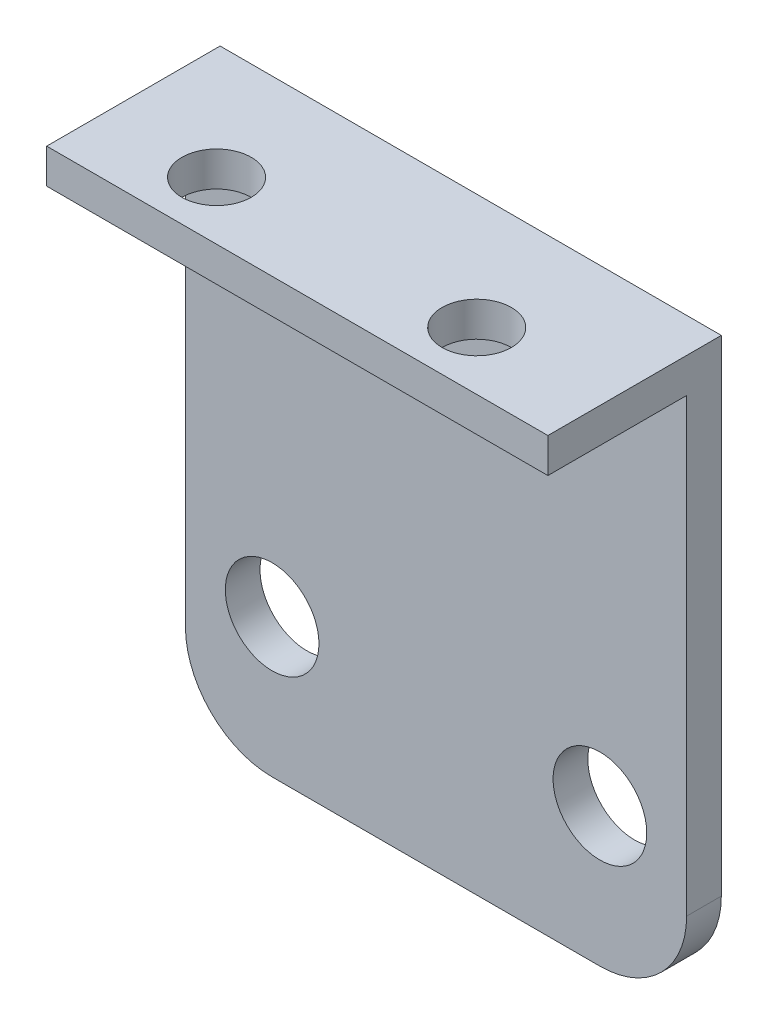
SolidWorks part; units mm, degrees
ref_plane "Front Plane" through (0, 0, 0) normal (0, 0, 1) x (1, 0, 0)
ref_plane "Top Plane" through (0, 0, 0) normal (0, 1, 0) x (1, 0, 0)
ref_plane "Right Plane" through (0, 0, 0) normal (1, 0, 0) x (0, 0, -1)
sketch "Sketch1" plane through (0, 0, 0) normal (0, 0, 1) x (1, 0, 0)
  line L1 (-13.5453, 41.5925) -> (15.3547, 41.5925)
  line L2 (-13.5453, 41.5925) -> (-13.5453, 74.5925)
  line L3 (-13.5453, 74.5925) -> (15.3547, 74.5925)
  line L4 (15.3547, 41.5925) -> (15.3547, 74.5925)
  circle A0 centre (-8.5453, 49.5925) radius 2.7
  circle A1 centre (10.3547, 49.5925) radius 2.7
  dimension "D1" = 5
  dimension "D2" = 5
  dimension "D3" = 8
  dimension "D4" = 25
extrude "Boss-Extrude1" add sketch "Sketch1" along normal blind 2
fillet "Fillet1" radius 5 2 edges at (-13.5453, 41.5925, 1) (15.3547, 41.5925, 1)
sketch "Sketch3" plane through (0, 0, 2) normal (0, 0, 1) x (1, 0, 0)
  line L0 (15.3547, 46.5925) -> (15.3547, 74.5925) construction
  line L1 (-13.5453, 74.5925) -> (15.3547, 74.5925)
  line L2 (-13.5453, 74.5925) -> (-13.5453, 72.5925)
  line L3 (-13.5453, 72.5925) -> (15.3547, 72.5925)
  line L4 (15.3547, 74.5925) -> (15.3547, 72.5925)
  dimension "D1" = 2
extrude "Boss-Extrude3" add sketch "Sketch3" along normal blind 8
sketch "Sketch5" plane through (0, 74.5925, 0) normal (0, 1, 0) x (1, 0, 0)
  circle A0 centre (-7.0916, -6.6582) radius 2
  circle A1 centre (7.9084, -6.6582) radius 2
extrude "Cut-Extrude2" cut sketch "Sketch5" against normal blind 10
